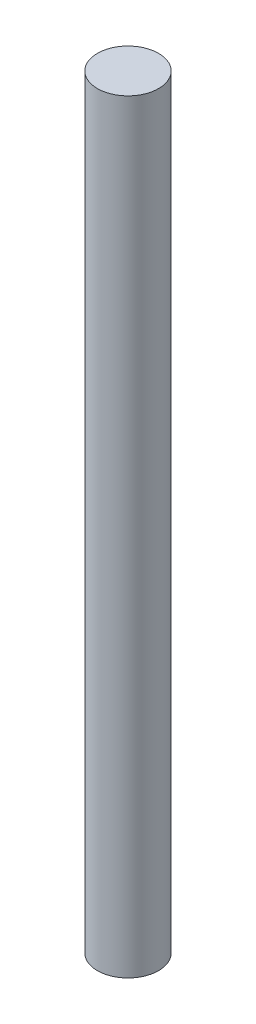
SolidWorks part; units mm, degrees
ref_plane "Front Plane" through (0, 0, 0) normal (0, 0, 1) x (1, 0, 0)
ref_plane "Top Plane" through (0, 0, 0) normal (0, 1, 0) x (1, 0, 0)
ref_plane "Right Plane" through (0, 0, 0) normal (1, 0, 0) x (0, 0, -1)
sketch "Sketch2" plane through (0, 0, 0) normal (0, 1, 0) x (1, 0, 0)
  circle A0 centre (0, 0) radius 4
extrude "Boss-Extrude1" add sketch "Sketch2" along normal blind 100
